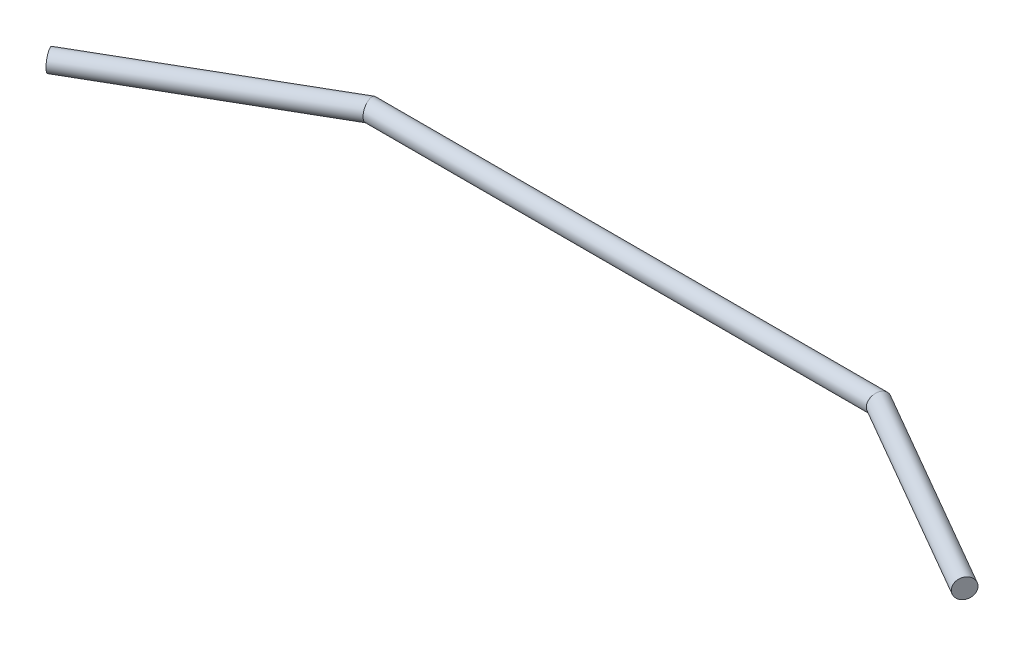
SolidWorks part; units mm, degrees
ref_plane "Plano frontal" through (0, 0, 0) normal (0, 0, 1) x (1, 0, 0)
ref_plane "Plano superior" through (0, 0, 0) normal (0, 1, 0) x (1, 0, 0)
ref_plane "Plano direito" through (0, 0, 0) normal (1, 0, 0) x (0, 0, -1)
sketch "Esboço8" plane through (0, 0, 0) normal (0, 1, 0) x (1, 0, 0)
  line L0 (32.5, 0) -> (-32.5, 0)
  line L1 (32.5, 0) -> (58.4808, -15)
  line L2 (0, -55) -> (0, 55) construction
  line L3 (-32.5, 0) -> (-58.4808, -15)
  point P9 (0, 0)
  dimension "D1" = 32.5
  dimension "D2" = 30
  dimension "D3" = 150
sweep "Varredura1" add path "Esboço8" circular profile diameter 2.5 parameters "D3"=2.5
